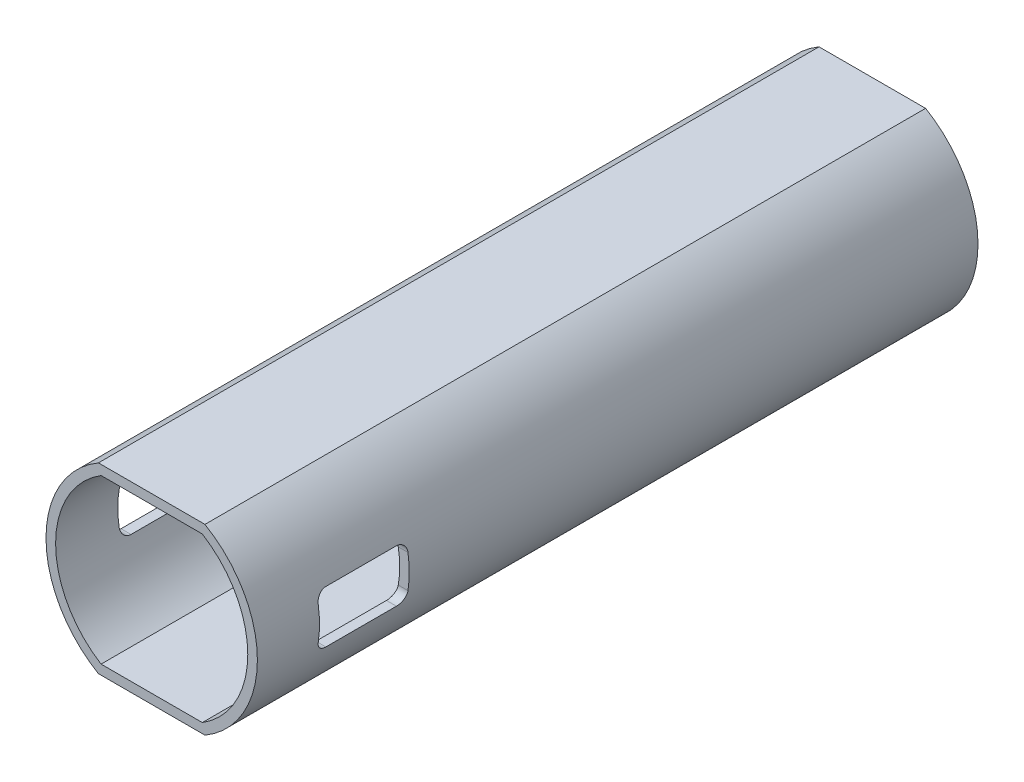
SolidWorks part; units mm, degrees
ref_plane "Front Plane" through (0, 0, 0) normal (0, 0, 1) x (1, 0, 0)
ref_plane "Top Plane" through (0, 0, 0) normal (0, 1, 0) x (1, 0, 0)
ref_plane "Right Plane" through (0, 0, 0) normal (1, 0, 0) x (0, 0, -1)
sketch "Sketch1" plane through (0, 0, 0) normal (0, 0, 1) x (1, 0, 0)
  line L0 (10.5357, 17) -> (-10.5357, 17)
  line L1 (-10.5357, -17) -> (10.5357, -17)
  line L2 (11.0905, 19) -> (-11.0905, 19)
  line L3 (-11.0905, -19) -> (11.0905, -19)
  arc A0 (-10.5357, 17) -> (-10.5357, -17) centre (0, 0) ccw
  arc A1 (10.5357, -17) -> (10.5357, 17) centre (0, 0) ccw
  arc A2 (-11.0905, 19) -> (-11.0905, -19) centre (0, 0) ccw
  arc A3 (11.0905, -19) -> (11.0905, 19) centre (0, 0) ccw
  dimension "D1" = 2
extrude "Boss-Extrude1" add sketch "Sketch1" along normal blind 150
sketch "Sketch2" plane through (0, 0, 0) normal (1, 0, 0) x (0, 0, -1)
  line L1 (-135.0636, 5.4478) -> (-120.3759, 5.4478)
  line L2 (-137.0636, 3.4478) -> (-137.0636, -3.4478)
  line L3 (-135.0636, -5.4478) -> (-120.3759, -5.4478)
  line L4 (-118.3759, 3.4478) -> (-118.3759, -3.4478)
  line L5 (-137.0636, 5.4478) -> (-118.3759, -5.4478) construction
  line L6 (-137.0636, -5.4478) -> (-118.3759, 5.4478) construction
  arc A0 (-137.0636, -3.4478) -> (-135.0636, -5.4478) centre (-135.0636, -3.4478) ccw
  arc A1 (-120.3759, -5.4478) -> (-118.3759, -3.4478) centre (-120.3759, -3.4478) ccw
  arc A2 (-120.3759, 5.4478) -> (-118.3759, 3.4478) centre (-120.3759, 3.4478) cw
  arc A3 (-135.0636, 5.4478) -> (-137.0636, 3.4478) centre (-135.0636, 3.4478) ccw
  point P0 (-127.7198, 0)
  dimension "D1" = 2
  dimension "D2" = 14.6878
  dimension "D3" = 6.8956
extrude "Cut-Extrude1" cut sketch "Sketch2" against normal through all both and the other way through all
scale "Scale1" bodies to scale 102 scale about centroid uniform scaling yes scale factor 0.5
